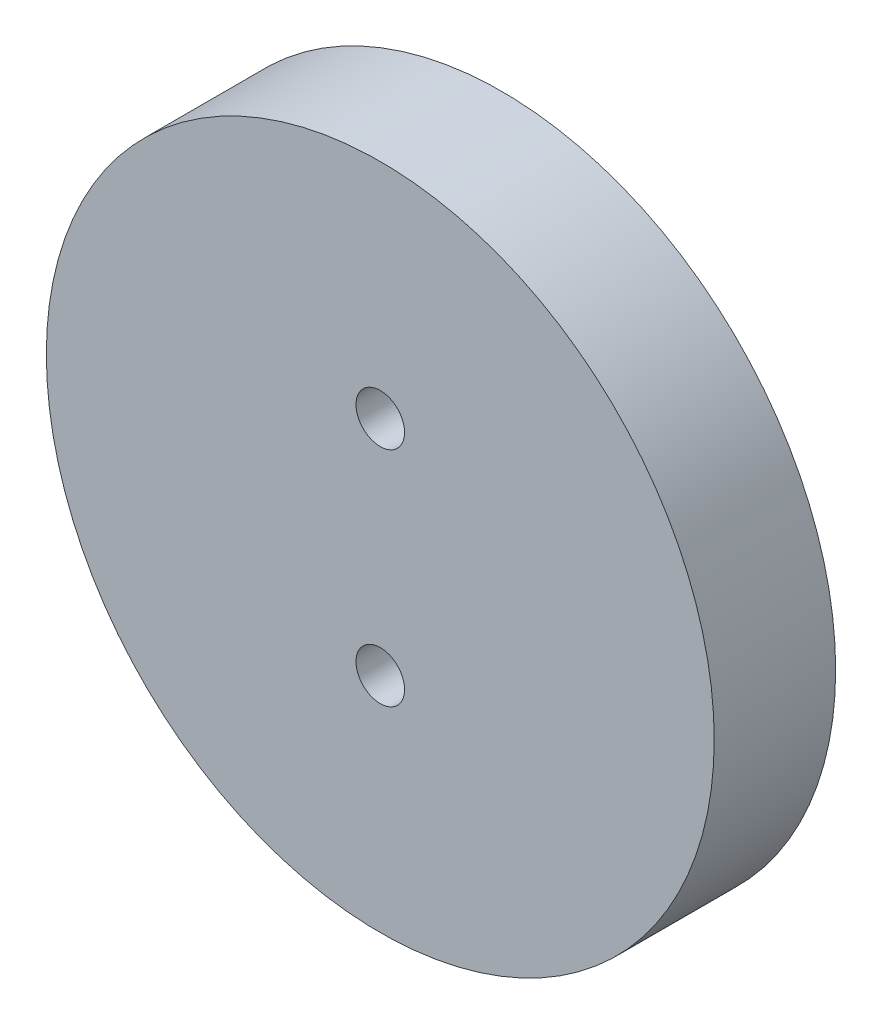
SolidWorks part; units mm, degrees
ref_plane "Front Plane" through (0, 0, 0) normal (0, 0, 1) x (1, 0, 0)
ref_plane "Top Plane" through (0, 0, 0) normal (0, 1, 0) x (1, 0, 0)
ref_plane "Right Plane" through (0, 0, 0) normal (1, 0, 0) x (0, 0, -1)
sketch "Sketch1" plane through (0, 0, 0) normal (0, 0, 1) x (1, 0, 0)
  circle A0 centre (0, 0) radius 34.925
  dimension "D1" = 69.85
extrude "Boss-Extrude1" add sketch "Sketch1" along normal blind 12.7
hole_wizard "CBORE for #10 Binding Head Machine Screw1" positions "Sketch2" profile "Sketch3" counterbore size "#10" standard "ANSI Inch" end condition through all
sketch "Sketch2" plane through (0, 0, 0) normal (0, 0, 1) x (1, 0, 0)
  line L0 (0, 34.925) -> (0, 11.6417) construction
  line L1 (0, 11.6417) -> (0, -11.6417) construction
  line L2 (0, -11.6417) -> (0, -34.925) construction
  circle A0 centre (0, 0) radius 34.925 construction
  point P0 (0, 11.6417)
  point P2 (0, -11.6417)
sketch "Sketch3" plane through (0, 11.6417, 0) normal (1, 0, 0) x (0, 1, 0)
  line L0 (0, 0) -> (0, 12.7)
  line L1 (0, 12.7) -> (2.54, 12.7)
  line L3 (2.54, 12.7) -> (2.54, 6.35)
  line L4 (2.54, 6.35) -> (5.5562, 6.35)
  line L5 (5.5562, 6.35) -> (5.5562, 0)
  line L7 (5.5562, 0) -> (0, 0)
  line L11 (0, -6.35) -> (0, 107.95) construction
  dimension "Thru Hole Dia." = 5.08
  dimension "Thru Hole Depth" = 12.7
  dimension "C'Bore Dia." = 11.1125
  dimension "C'Bore Depth" = 6.35
